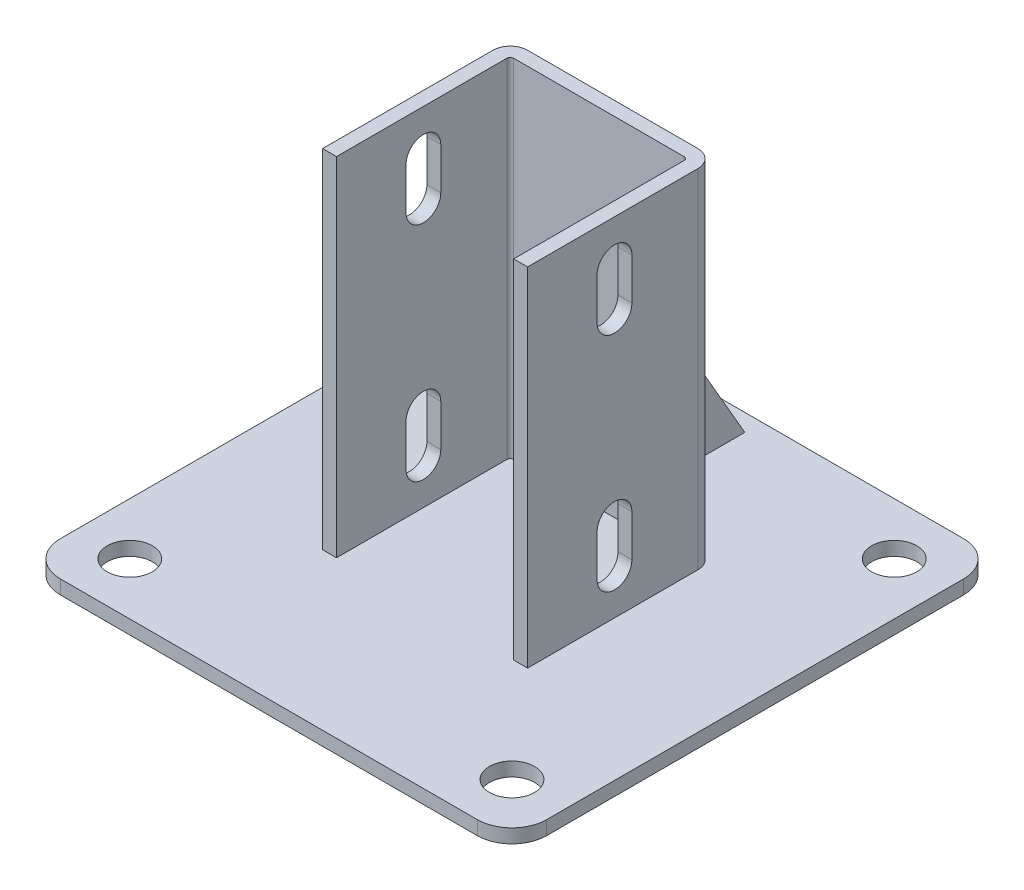
SolidWorks part; units mm, degrees
material "Ст3пс ГОСТ 380-2005"
ref_plane "Спереди" through (0, 0, 0) normal (0, 0, 1) x (1, 0, 0)
ref_plane "Сверху" through (0, 0, 0) normal (0, 1, 0) x (1, 0, 0)
ref_plane "Справа" through (0, 0, 0) normal (1, 0, 0) x (0, 0, -1)
sketch "Эскиз2" plane through (0, 0, 0) normal (0, 1, 0) x (1, 0, 0)
  line L1 (-70, -70) -> (70, -70)
  line L2 (-70, -70) -> (-70, 70)
  line L3 (-70, 70) -> (70, 70)
  line L4 (70, -70) -> (70, 70)
  line L5 (-70, -70) -> (70, 70) construction
  line L6 (-70, 70) -> (70, -70) construction
  point P0 (0, 0)
  dimension "D1" = 140
extrude "Бобышка-Вытянуть1" add sketch "Эскиз2" along normal blind 4
sketch "Эскиз3" plane through (0, 4, 0) normal (0, 1, 0) x (1, 0, 0)
  line L0 (-25.5, -25) -> (-25.5, 25)
  line L1 (-25.5, 25) -> (25.5, 25)
  line L2 (25.5, 25) -> (25.5, -25)
  point P2 (0, 25)
  point P5 (-25.5, 0)
  dimension "D2" = 51
  dimension "D3" = 50
extrude "Вытянуть-Тонкостенный1" add sketch "Эскиз3" along normal offset from surface (100 mm away) 104 thin up to face at (0, 0, 0) thin type one direction reverse wall 4
sketch "Эскиз4" plane through (0, 0, 0) normal (1, 0, 0) x (0, 0, -1)
  line L0 (29, 66.3538) -> (65, 4)
  line L1 (29, 104) -> (29, 4) construction
  line L2 (-70, 4) -> (70, 4) construction
  line L3 (65, 4) -> (29, 4)
  line L4 (29, 4) -> (29, 66.3538)
  line L5 (70, 4) -> (70, 0) construction
  dimension "D1" = 30
  dimension "D2" = 5
extrude "Бобышка-Вытянуть2" add sketch "Эскиз4" along normal mid plane 4
sketch "Эскиз5" plane through (29.5, 0, 0) normal (1, 0, 0) x (0, 0, -1)
  line L0 (0, 92) -> (0, 80) construction
  line L1 (5, 92) -> (5, 80)
  line L2 (-5, 92) -> (-5, 80)
  line L3 (0, 28) -> (0, 16) construction
  line L4 (5, 28) -> (5, 16)
  line L5 (-5, 28) -> (-5, 16)
  line L6 (-25, 104) -> (24, 104) construction
  line L7 (-70, 4) -> (70, 4) construction
  arc A0 (5, 92) -> (-5, 92) centre (0, 92) ccw
  arc A1 (-5, 80) -> (5, 80) centre (0, 80) ccw
  arc A2 (5, 28) -> (-5, 28) centre (0, 28) ccw
  arc A3 (-5, 16) -> (5, 16) centre (0, 16) ccw
  point P3 (0, 86)
  point P8 (0, 22)
  dimension "D2" = 12
  dimension "D4" = 12
  dimension "D1" = 10
  dimension "D3" = 12
extrude "Вырез-Вытянуть1" cut sketch "Эскиз5" against normal through all
sketch "Эскиз6" plane through (0, 4, 0) normal (0, 1, 0) x (1, 0, 0)
  line L0 (-70, 70) -> (-70, -70) construction
  line L1 (55, -55) -> (-55, -55) construction
  line L2 (55, -55) -> (55, 55) construction
  line L3 (55, 55) -> (-55, 55) construction
  line L4 (-55, -55) -> (-55, 55) construction
  line L5 (55, -55) -> (-55, 55) construction
  line L6 (55, 55) -> (-55, -55) construction
  line L7 (70, 70) -> (-70, 70) construction
  circle A0 centre (-55, 55) radius 6.5
  circle A1 centre (-55, -55) radius 6.5
  circle A2 centre (55, 55) radius 6.5
  circle A3 centre (55, -55) radius 6.5
  point P0 (0, 0)
  dimension "D1" = 13
  dimension "D2" = 15
  dimension "D3" = 15
extrude "Вырез-Вытянуть2" cut sketch "Эскиз6" against normal through all
fillet "Скругление1" radius 10 4 edges at (70, 2, 70) (-70, 2, 70) (-70, 2, -70) (70, 2, -70)
